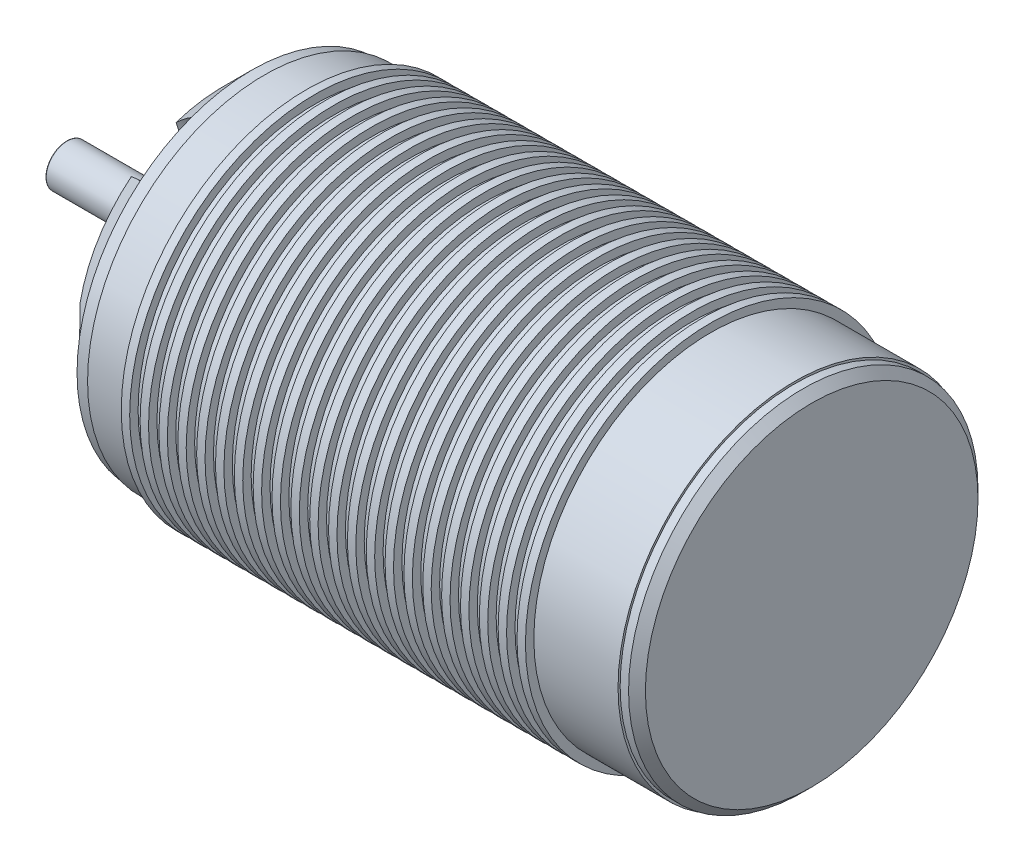
SolidWorks part; units mm, degrees
ref_plane "Front" through (0, 0, 0) normal (0, 0, 1) x (1, 0, 0)
ref_plane "Top" through (0, 0, 0) normal (0, 1, 0) x (1, 0, 0)
ref_plane "Right" through (0, 0, 0) normal (1, 0, 0) x (0, 0, -1)
sketch "Sketch2" plane through (0, 0, 0) normal (0, 1, 0) x (1, 0, 0)
  line L0 (-23.2619, 21) -> (-23.2619, 22)
  line L1 (-31.5, 0) -> (31.5, 0)
  line L3 (-31.5, 21) -> (-26.5, 21)
  line L5 (-31.5, 0) -> (31.5, 21) construction
  line L6 (-31.5, 21) -> (31.5, 0) construction
  line L7 (-24.2619, 22) -> (-23.2619, 22)
  line L8 (-26.5, 21) -> (-26.5, 22)
  line L9 (-26.5, 22) -> (-25.5, 22)
  line L10 (-25.5, 21) -> (-25.5, 22)
  line L11 (-24.2619, 21) -> (-24.2619, 22)
  line L12 (-21.0238, 21) -> (-21.0238, 22)
  line L13 (-22.0238, 22) -> (-21.0238, 22)
  line L14 (-22.0238, 21) -> (-22.0238, 22)
  line L15 (-18.7857, 21) -> (-18.7857, 22)
  line L16 (-19.7857, 22) -> (-18.7857, 22)
  line L17 (-19.7857, 21) -> (-19.7857, 22)
  line L18 (-16.5476, 21) -> (-16.5476, 22)
  line L19 (-17.5476, 22) -> (-16.5476, 22)
  line L20 (-17.5476, 21) -> (-17.5476, 22)
  line L21 (-14.3095, 21) -> (-14.3095, 22)
  line L22 (-15.3095, 22) -> (-14.3095, 22)
  line L23 (-15.3095, 21) -> (-15.3095, 22)
  line L24 (-12.0714, 21) -> (-12.0714, 22)
  line L25 (-13.0714, 22) -> (-12.0714, 22)
  line L26 (-13.0714, 21) -> (-13.0714, 22)
  line L27 (-9.8333, 21) -> (-9.8333, 22)
  line L28 (-10.8333, 22) -> (-9.8333, 22)
  line L29 (-10.8333, 21) -> (-10.8333, 22)
  line L30 (-7.5952, 21) -> (-7.5952, 22)
  line L31 (-8.5952, 22) -> (-7.5952, 22)
  line L32 (-8.5952, 21) -> (-8.5952, 22)
  line L33 (-5.3571, 21) -> (-5.3571, 22)
  line L34 (-6.3571, 22) -> (-5.3571, 22)
  line L35 (-6.3571, 21) -> (-6.3571, 22)
  line L36 (-3.119, 21) -> (-3.119, 22)
  line L37 (-4.119, 22) -> (-3.119, 22)
  line L38 (-4.119, 21) -> (-4.119, 22)
  line L39 (-0.881, 21) -> (-0.881, 22)
  line L40 (-1.881, 22) -> (-0.881, 22)
  line L41 (-1.881, 21) -> (-1.881, 22)
  line L42 (1.3571, 21) -> (1.3571, 22)
  line L43 (0.3571, 22) -> (1.3571, 22)
  line L44 (0.3571, 21) -> (0.3571, 22)
  line L45 (3.5952, 21) -> (3.5952, 22)
  line L46 (2.5952, 22) -> (3.5952, 22)
  line L47 (2.5952, 21) -> (2.5952, 22)
  line L48 (5.8333, 21) -> (5.8333, 22)
  line L49 (4.8333, 22) -> (5.8333, 22)
  line L50 (4.8333, 21) -> (4.8333, 22)
  line L51 (8.0714, 21) -> (8.0714, 22)
  line L52 (7.0714, 22) -> (8.0714, 22)
  line L53 (7.0714, 21) -> (7.0714, 22)
  line L54 (10.3095, 21) -> (10.3095, 22)
  line L55 (9.3095, 22) -> (10.3095, 22)
  line L56 (9.3095, 21) -> (9.3095, 22)
  line L57 (12.5476, 21) -> (12.5476, 22)
  line L58 (11.5476, 22) -> (12.5476, 22)
  line L59 (11.5476, 21) -> (11.5476, 22)
  line L60 (14.7857, 21) -> (14.7857, 22)
  line L61 (13.7857, 22) -> (14.7857, 22)
  line L62 (13.7857, 21) -> (13.7857, 22)
  line L63 (17.0238, 21) -> (17.0238, 22)
  line L64 (16.0238, 22) -> (17.0238, 22)
  line L65 (16.0238, 21) -> (16.0238, 22)
  line L66 (19.2619, 21) -> (19.2619, 22)
  line L67 (18.2619, 22) -> (19.2619, 22)
  line L68 (18.2619, 21) -> (18.2619, 22)
  line L69 (21.5, 21) -> (21.5, 22)
  line L70 (20.5, 22) -> (21.5, 22)
  line L71 (20.5, 21) -> (20.5, 22)
  line L74 (-25.5, 21) -> (-24.2619, 21)
  line L80 (-31.5, 0) -> (-31.5, 21)
  line L81 (-23.2619, 21) -> (-22.0238, 21)
  line L82 (-21.0238, 21) -> (-19.7857, 21)
  line L83 (-18.7857, 21) -> (-17.5476, 21)
  line L84 (-16.5476, 21) -> (-15.3095, 21)
  line L85 (-14.3095, 21) -> (-13.0714, 21)
  line L86 (-12.0714, 21) -> (-10.8333, 21)
  line L87 (-9.8333, 21) -> (-8.5952, 21)
  line L88 (-7.5952, 21) -> (-6.3571, 21)
  line L89 (-5.3571, 21) -> (-4.119, 21)
  line L90 (-3.119, 21) -> (-1.881, 21)
  line L91 (-0.881, 21) -> (0.3571, 21)
  line L92 (1.3571, 21) -> (2.5952, 21)
  line L93 (3.5952, 21) -> (4.8333, 21)
  line L94 (5.8333, 21) -> (7.0714, 21)
  line L95 (8.0714, 21) -> (9.3095, 21)
  line L96 (10.3095, 21) -> (11.5476, 21)
  line L97 (12.5476, 21) -> (13.7857, 21)
  line L98 (14.7857, 21) -> (16.0238, 21)
  line L99 (17.0238, 21) -> (18.2619, 21)
  line L100 (19.2619, 21) -> (20.5, 21)
  line L101 (21.5, 21) -> (31.5, 21)
  line L102 (31.5, 21) -> (31.5, 0)
  point P0 (0, 10.5)
  dimension "D1" = 5
  dimension "D2" = 63
  dimension "D3" = 21
  dimension "D4" = 1
  dimension "D5" = 1
  dimension "D8" = 10
  dimension "D6" = 22
revolve "Revolve1" add sketch "Sketch2" angle 360 about L1
sketch "Sketch3" plane through (31.5, 0, 0) normal (1, 0, 0) x (0, 0, -1)
  circle A0 centre (0, 0) radius 20.75
extrude "Boss-Extrude1" add sketch "Sketch3" along normal blind 2
sketch "Sketch4" plane through (-31.5, 0, 0) normal (-1, 0, 0) x (0, 0, 1)
  circle A0 centre (0, 0) radius 20.75
extrude "Boss-Extrude2" add sketch "Sketch4" along normal blind 5
chamfer "Chamfer1" distance 3.5 angle 45 1 edges at (-36.5, 0, 20.75)
chamfer "Chamfer2" distance 1 angle 45 1 edges at (33.5, 0, -20.75)
ref_plane "Plane1" through (-33, 0, 0) normal (1, 0, 0) x (0, 0, -1)
sketch "Sketch6" plane through (-33, 0, 0) normal (1, 0, 0) x (0, 0, -1)
  line L0 (0, 0) -> (-20.75, 0) construction
  line L1 (0, 0) -> (-10.375, 17.97) construction
  line L2 (0, 0) -> (-10.375, -17.97) construction
  line L3 (-10.375, 0) -> (-10.5562, -1.9918) construction
  arc A0 (-7.1953, 19.4625) -> (-13.2574, 15.9625) centre (0, 0) ccw
  arc A1 (-20.4527, 3.5) -> (-20.4527, -3.5) centre (0, 0) ccw
  circle A2 centre (0, 0) radius 20.75 construction
  arc A3 (-13.2574, -15.9625) -> (-7.1953, -19.4625) centre (0, 0) ccw
  arc A4 (7.1953, -19.4625) -> (13.2574, -15.9625) centre (0, 0) ccw
  arc A5 (20.4527, -3.5) -> (20.4527, 3.5) centre (0, 0) ccw
  arc A6 (13.2574, 15.9625) -> (7.1953, 19.4625) centre (0, 0) ccw
  circle A7 centre (0, 0) radius 4.5
  spline S0 degree 3 poles (-20.4527, 3.5) (-15.8642, 4.1903) (-10.608, 0.9773) (-10.2531, -0.4533) (-10.1939, -2.0869) (-11.4403, -1.8524) (-16.7298, -2.3122) (-20.4527, -3.5) knots 0 0 0 0 0.324704 0.382256 0.554047 0.617969 1 1 1 1
  spline S1 degree 3 poles (-7.1953, 19.4625) (-4.3032, 15.834) (-4.4577, 9.6754) (-5.5191, 8.6528) (-6.9043, 7.7848) (-7.3243, 8.9814) (-10.3673, 13.3323) (-13.2574, 15.9625) knots 0 0 0 0 0.324704 0.382256 0.554047 0.617969 1 1 1 1
  spline S2 degree 3 poles (13.2574, 15.9625) (11.561, 11.6437) (6.1503, 8.6982) (4.734, 9.1061) (3.2897, 9.8717) (4.1159, 10.8337) (6.3625, 15.6445) (7.1953, 19.4625) knots 0 0 0 0 0.324704 0.382256 0.554047 0.617969 1 1 1 1
  spline S3 degree 3 poles (20.4527, -3.5) (15.8642, -4.1903) (10.608, -0.9773) (10.2531, 0.4533) (10.1939, 2.0869) (11.4403, 1.8524) (16.7298, 2.3122) (20.4527, 3.5) knots 0 0 0 0 0.324704 0.382256 0.554047 0.617969 1 1 1 1
  spline S4 degree 3 poles (7.1953, -19.4625) (4.3032, -15.834) (4.4577, -9.6754) (5.5191, -8.6528) (6.9043, -7.7848) (7.3243, -8.9814) (10.3673, -13.3323) (13.2574, -15.9625) knots 0 0 0 0 0.324704 0.382256 0.554047 0.617969 1 1 1 1
  spline S5 degree 3 poles (-13.2574, -15.9625) (-11.561, -11.6437) (-6.1503, -8.6982) (-4.734, -9.1061) (-3.2897, -9.8717) (-4.1159, -10.8337) (-6.3625, -15.6445) (-7.1953, -19.4625) knots 0 0 0 0 0.324704 0.382256 0.554047 0.617969 1 1 1 1
  point P6 (-10.375, 0)
  point P11 (-20.4527, 3.5)
  point P12 (-20.4527, -3.5)
  point P40 (0, 0)
  dimension "D4" = 41.5
  dimension "D5" = 3.5
  dimension "D1" = 60
  dimension "D2" = 60
  dimension "D3" = 3.5
extrude "Cut-Extrude1" cut sketch "Sketch6" against normal blind 22
sketch "Sketch5" plane through (-33, 0, 0) normal (1, 0, 0) x (0, 0, -1)
  circle A0 centre (0, 0) radius 2.5
extrude "Boss-Extrude3" add sketch "Sketch5" against normal blind 22
sketch "Sketch7" plane through (-36.5, 0, 0) normal (-1, 0, 0) x (0, 0, 1)
  line L0 (0, 0) -> (31.9499, 0) construction
  line L1 (0, 0) -> (27.6694, 15.9749) construction
  line L3 (0, 0) -> (-27.6694, 15.9749) construction
  line L4 (0, 0) -> (-27.6694, -15.9749) construction
  line L5 (0, 0) -> (27.6694, -15.9749) construction
  circle A0 centre (0, 0) radius 12.5 construction
  point P4 (10.8253, 6.25)
  point P9 (10.8253, -6.25)
  point P11 (-10.8253, -6.25)
  point P12 (-10.8253, 6.25)
  dimension "D1" = 30
  dimension "D2" = 120
  dimension "D3" = 60
  dimension "D4" = 30
  dimension "D5" = 25
hole_wizard "M3x0.5 Tapped Hole1" positions "Sketch9" profile "Sketch10" tap size "M3x0.5" standard "ANSI Metric"
sketch "Sketch9" plane through (-36.5, 0, 0) normal (-1, 0, 0) x (0, 0, 1)
  circle A0 centre (0, 0) radius 12.5 construction
  point P0 (-10.8253, 6.25)
  point P3 (-10.8253, -6.25)
  point P6 (10.8253, -6.25)
  point P10 (10.8253, 6.25)
sketch "Sketch10" plane through (-36.5, 6.25, -10.8253) normal (0, 1, 0) x (0, 0, 1)
  line L0 (0, 0) -> (0, 8.2511)
  line L1 (0, 8.2511) -> (1.25, 7.5)
  line L2 (1.25, 7.5) -> (1.25, 0)
  line L5 (1.25, 0) -> (0, 0)
  line L10 (0, 8.2511) -> (-1.25, 7.5) construction
  line L11 (0, -6.35) -> (0, 107.95) construction
  dimension "Tap Drill Dia." = 2.5
  dimension "Tap Drill Depth" = 7.5
  dimension "Drill Angle" = 118
cosmetic thread "Hole Thread1" parameters "D1"=6, "D2"=3
cosmetic thread "Hole Thread2" parameters "D1"=6, "D2"=3
cosmetic thread "Hole Thread3" parameters "D1"=6, "D2"=3
cosmetic thread "Hole Thread4" parameters "D1"=6, "D2"=3
sketch "Sketch11" plane through (-36.5, 0, 0) normal (-1, 0, 0) x (0, 0, 1)
  line L0 (0, 23.8525) -> (0, -26.546) construction
  circle A0 centre (0, 0) radius 12.5 construction
  point P3 (0, 12.5)
  point P4 (0, -12.5)
hole_wizard "M4x0.7 Tapped Hole1" positions "Sketch13" profile "Sketch12" tap size "M4x0.7" standard "ANSI Metric"
sketch "Sketch13" plane through (-36.5, 0, 0) normal (-1, 0, 0) x (0, 0, 1)
  point P0 (0, 12.5)
  point P3 (0, -12.5)
sketch "Sketch12" plane through (-36.5, 12.5, 0) normal (0, 1, 0) x (0, 0, 1)
  line L0 (0, 0) -> (0, 11.0914)
  line L1 (0, 11.0914) -> (1.65, 10.1)
  line L2 (1.65, 10.1) -> (1.65, 0)
  line L5 (1.65, 0) -> (0, 0)
  line L10 (0, 11.0914) -> (-1.65, 10.1) construction
  line L11 (0, -6.35) -> (0, 107.95) construction
  dimension "Tap Drill Dia." = 3.3
  dimension "Tap Drill Depth" = 10.1
  dimension "Drill Angle" = 118
cosmetic thread "Hole Thread5" parameters "D1"=8, "D2"=4
cosmetic thread "Hole Thread6" parameters "D1"=8, "D2"=4
chamfer "Chamfer3" [suppressed] distance 0.25 angle 45
chamfer "Chamfer4" [suppressed] distance 0.5 angle 45
chamfer "Chamfer5" [suppressed] distance 0.25 angle 45
sketch "Sketch14" [suppressed] plane through (-55, 0, 0) normal (-1, 0, 0) x (0, 0, 1)
  line L0 (-1.9649, 1.5457) -> (2.034, 1.4535)
  line L1 (-1.9649, 1.5457) -> (-1.9228, 3.3745)
  line L2 (-1.9228, 3.3745) -> (2.0762, 3.2823)
  line L3 (2.0762, 3.2823) -> (2.034, 1.4535)
  circle A0 centre (0, 0) radius 2.5 construction
extrude "Cut-Extrude2" [suppressed] cut sketch "Sketch14" against normal blind 16
fillet "Fillet1" [suppressed] radius 0.1
fillet "Fillet2" radius 0.1 1 edges at (-55, 0, -2.5)
